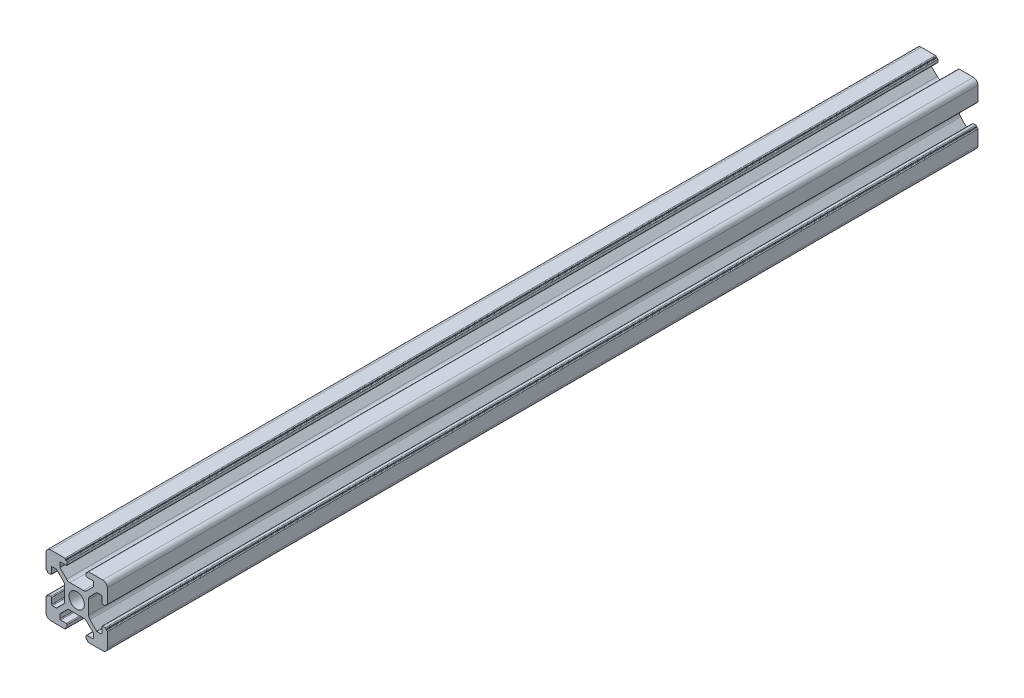
SolidWorks part; units mm, degrees
ref_plane "前视基准面" through (0, 0, 0) normal (0, 0, 1) x (1, 0, 0)
ref_plane "上视基准面" through (0, 0, 0) normal (0, 1, 0) x (1, 0, 0)
ref_plane "右视基准面" through (0, 0, 0) normal (1, 0, 0) x (0, 0, -1)
sketch "草图1" plane through (0, 0, 0) normal (0, 0, 1) x (1, 0, 0)
  line L0 (0, 0) -> (0, 5.5) construction
  line L1 (-8.5023, -10.0023) -> (-3.85, -10.0023)
  line L2 (-10.0023, -8.5023) -> (-10.0023, -3.85)
  line L3 (-8.5023, 10.0023) -> (-3.85, 10.0023)
  line L4 (10.0023, -8.5023) -> (10.0023, -3.85)
  line L5 (-10.0023, -10.0023) -> (10.0023, 10.0023) construction
  line L6 (-10.0023, 10.0023) -> (10.0023, -10.0023) construction
  line L7 (-2.218, -3.9) -> (2.218, -3.9)
  line L8 (-3.9, -2.218) -> (-3.9, 2.218)
  line L9 (-2.218, 3.9) -> (2.218, 3.9)
  line L10 (3.9, -2.218) -> (3.9, 2.218)
  line L11 (-3.9, -3.9) -> (3.9, 3.9) construction
  line L12 (-3.9, 3.9) -> (3.9, -3.9) construction
  line L13 (-5.25, -8.2) -> (-3.35, -8.2)
  line L14 (-8.2, -5.25) -> (-8.2, -3.35)
  line L15 (-5.25, 8.2) -> (-3.35, 8.2)
  line L16 (8.2, -5.25) -> (8.2, -3.35)
  line L17 (-8.2, -8.2) -> (8.2, 8.2) construction
  line L18 (-8.2, 8.2) -> (8.2, -8.2) construction
  line L19 (-7.95, 5.5) -> (-6.6642, 5.5)
  line L20 (0, 0) -> (5.5, 0) construction
  line L23 (-5.5, 7.95) -> (-5.5, 6.6642)
  line L26 (0, 0) -> (-0.5303, 0.5303)
  line L27 (3.2787, 4.3393) -> (5.4268, 6.4874)
  line L28 (0, 0) -> (0.5303, -0.5303)
  line L29 (5.5, 6.6642) -> (5.5, 7.95)
  line L30 (4.3393, 3.2787) -> (6.4874, 5.4268)
  line L31 (6.6642, 5.5) -> (7.95, 5.5)
  line L32 (4.3393, -3.2787) -> (6.4874, -5.4268)
  line L33 (3.2787, -4.3393) -> (5.4268, -6.4874)
  line L34 (-3.2787, -4.3393) -> (-5.4268, -6.4874)
  line L35 (-4.3393, -3.2787) -> (-6.4874, -5.4268)
  line L36 (-4.3393, 3.2787) -> (-6.4874, 5.4268)
  line L37 (-3.2787, 4.3393) -> (-5.4268, 6.4874)
  line L38 (3.1, -8.45) -> (3.1, -9.2523)
  line L39 (8.45, 3.1) -> (9.2523, 3.1)
  line L40 (-5.5, -6.6642) -> (-5.5, -7.95)
  line L41 (-6.6642, -5.5) -> (-7.95, -5.5)
  line L42 (5.5, -6.6642) -> (5.5, -7.95)
  line L43 (6.6642, -5.5) -> (7.95, -5.5)
  line L44 (9.2523, -3.1) -> (8.45, -3.1)
  line L46 (10.0023, 3.85) -> (10.0023, 8.5023)
  line L47 (8.2, 3.35) -> (8.2, 5.25)
  line L48 (-3.1, -9.2523) -> (-3.1, -8.45)
  line L49 (-8.45, -3.1) -> (-9.2523, -3.1)
  line L50 (-9.2523, 3.1) -> (-8.45, 3.1)
  line L51 (-3.1, 8.45) -> (-3.1, 9.2523)
  line L52 (3.1, 9.2523) -> (3.1, 8.45)
  line L53 (3.85, 10.0023) -> (8.5023, 10.0023)
  line L54 (3.35, 8.2) -> (5.25, 8.2)
  line L55 (-10.0023, 3.85) -> (-10.0023, 8.5023)
  line L56 (-8.2, 3.35) -> (-8.2, 5.25)
  line L57 (3.35, -8.2) -> (5.25, -8.2)
  line L58 (3.85, -10.0023) -> (8.5023, -10.0023)
  line L59 (9.7523, -3.6) -> (9.5023, -3.6)
  line L61 (9.7523, 3.6) -> (9.5023, 3.6)
  line L62 (9.5023, -3.6) -> (9.5023, -3.35)
  line L63 (3.6, -9.7523) -> (3.6, -9.5023)
  line L64 (3.35, -9.5023) -> (3.6, -9.5023)
  line L65 (9.5023, 3.35) -> (9.5023, 3.6)
  line L66 (-3.6, -9.5023) -> (-3.35, -9.5023)
  line L67 (-3.6, -9.7523) -> (-3.6, -9.5023)
  line L68 (-9.7523, -3.6) -> (-9.5023, -3.6)
  line L69 (-9.5023, -3.35) -> (-9.5023, -3.6)
  line L70 (-9.5023, 3.6) -> (-9.5023, 3.35)
  line L71 (-9.7523, 3.6) -> (-9.5023, 3.6)
  line L72 (-3.6, 9.7523) -> (-3.6, 9.5023)
  line L73 (-3.35, 9.5023) -> (-3.6, 9.5023)
  line L74 (3.6, 9.5023) -> (3.35, 9.5023)
  line L75 (3.6, 9.7523) -> (3.6, 9.5023)
  circle A0 centre (0, 0) radius 2.5
  arc A1 (10.0023, 8.5023) -> (8.5023, 10.0023) centre (8.5023, 8.5023) ccw
  arc A2 (8.5023, -10.0023) -> (10.0023, -8.5023) centre (8.5023, -8.5023) ccw
  arc A3 (-10.0023, -8.5023) -> (-8.5023, -10.0023) centre (-8.5023, -8.5023) ccw
  arc A4 (-10.0023, 8.5023) -> (-8.5023, 10.0023) centre (-8.5023, 8.5023) cw
  arc A5 (-9.5023, -3.35) -> (-9.2523, -3.1) centre (-9.2523, -3.35) cw
  arc A6 (-9.7523, -3.6) -> (-10.0023, -3.85) centre (-9.7523, -3.85) ccw
  arc A7 (-8.45, -3.1) -> (-8.2, -3.35) centre (-8.45, -3.35) cw
  arc A8 (-7.95, -5.5) -> (-8.2, -5.25) centre (-7.95, -5.25) cw
  arc A9 (-6.4874, -5.4268) -> (-6.6642, -5.5) centre (-6.6642, -5.25) cw
  arc A10 (-5.4268, -6.4874) -> (-5.5, -6.6642) centre (-5.25, -6.6642) ccw
  arc A11 (-5.5, -7.95) -> (-5.25, -8.2) centre (-5.25, -7.95) ccw
  arc A12 (-3.6, -9.7523) -> (-3.85, -10.0023) centre (-3.85, -9.7523) cw
  arc A13 (-3.35, -9.5023) -> (-3.1, -9.2523) centre (-3.35, -9.2523) ccw
  arc A14 (-3.1, -8.45) -> (-3.35, -8.2) centre (-3.35, -8.45) ccw
  arc A15 (3.1, -8.45) -> (3.35, -8.2) centre (3.35, -8.45) cw
  arc A16 (5.5, -7.95) -> (5.25, -8.2) centre (5.25, -7.95) cw
  arc A17 (5.4268, -6.4874) -> (5.5, -6.6642) centre (5.25, -6.6642) cw
  arc A18 (6.4874, -5.4268) -> (6.6642, -5.5) centre (6.6642, -5.25) ccw
  arc A19 (7.95, -5.5) -> (8.2, -5.25) centre (7.95, -5.25) ccw
  arc A20 (8.45, -3.1) -> (8.2, -3.35) centre (8.45, -3.35) ccw
  arc A21 (9.5023, -3.35) -> (9.2523, -3.1) centre (9.2523, -3.35) ccw
  arc A22 (9.7523, -3.6) -> (10.0023, -3.85) centre (9.7523, -3.85) cw
  arc A23 (3.35, -9.5023) -> (3.1, -9.2523) centre (3.35, -9.2523) cw
  arc A24 (3.6, -9.7523) -> (3.85, -10.0023) centre (3.85, -9.7523) ccw
  arc A25 (7.95, 5.5) -> (8.2, 5.25) centre (7.95, 5.25) cw
  arc A26 (8.2, 3.35) -> (8.45, 3.1) centre (8.45, 3.35) ccw
  arc A27 (9.5023, 3.35) -> (9.2523, 3.1) centre (9.2523, 3.35) cw
  arc A28 (9.7523, 3.6) -> (10.0023, 3.85) centre (9.7523, 3.85) ccw
  arc A29 (6.6642, 5.5) -> (6.4874, 5.4268) centre (6.6642, 5.25) ccw
  arc A30 (5.4268, 6.4874) -> (5.5, 6.6642) centre (5.25, 6.6642) ccw
  arc A31 (5.5, 7.95) -> (5.25, 8.2) centre (5.25, 7.95) ccw
  arc A32 (3.1, 8.45) -> (3.35, 8.2) centre (3.35, 8.45) ccw
  arc A33 (3.6, 9.7523) -> (3.85, 10.0023) centre (3.85, 9.7523) cw
  arc A34 (3.35, 9.5023) -> (3.1, 9.2523) centre (3.35, 9.2523) ccw
  arc A35 (-9.7523, 3.6) -> (-10.0023, 3.85) centre (-9.7523, 3.85) cw
  arc A36 (-9.5023, 3.35) -> (-9.2523, 3.1) centre (-9.2523, 3.35) ccw
  arc A37 (-8.45, 3.1) -> (-8.2, 3.35) centre (-8.45, 3.35) ccw
  arc A38 (-8.2, 5.25) -> (-7.95, 5.5) centre (-7.95, 5.25) cw
  arc A39 (-6.4874, 5.4268) -> (-6.6642, 5.5) centre (-6.6642, 5.25) ccw
  arc A40 (-5.4268, 6.4874) -> (-5.5, 6.6642) centre (-5.25, 6.6642) cw
  arc A41 (-5.5, 7.95) -> (-5.25, 8.2) centre (-5.25, 7.95) cw
  arc A42 (-3.1, 8.45) -> (-3.35, 8.2) centre (-3.35, 8.45) cw
  arc A43 (-3.1, 9.2523) -> (-3.35, 9.5023) centre (-3.35, 9.2523) ccw
  arc A44 (-3.6, 9.7523) -> (-3.85, 10.0023) centre (-3.85, 9.7523) ccw
  arc A45 (-4.3393, 3.2787) -> (-3.9, 2.218) centre (-5.4, 2.218) cw
  arc A46 (-3.2787, 4.3393) -> (-2.218, 3.9) centre (-2.218, 5.4) ccw
  arc A47 (3.2787, 4.3393) -> (2.218, 3.9) centre (2.218, 5.4) cw
  arc A48 (4.3393, 3.2787) -> (3.9, 2.218) centre (5.4, 2.218) ccw
  arc A49 (4.3393, -3.2787) -> (3.9, -2.218) centre (5.4, -2.218) cw
  arc A50 (3.2787, -4.3393) -> (2.218, -3.9) centre (2.218, -5.4) ccw
  arc A51 (-4.3393, -3.2787) -> (-3.9, -2.218) centre (-5.4, -2.218) ccw
  arc A52 (-2.218, -3.9) -> (-3.2787, -4.3393) centre (-2.218, -5.4) ccw
  point P0 (0, 0)
  point P7 (10.0023, 0)
  point P62 (0, 0)
  point P76 (0, 0)
  point P92 (-8.2, -5.5)
  point P99 (0, 0)
  point P106 (-5.5, -8.2)
  point P117 (5.5, -8.2)
  point P124 (8.2, -5.5)
  point P137 (8.2, 5.5)
  point P140 (8.2, 3.1)
  point P147 (6.5607, 5.5)
  point P152 (5.5, 8.2)
  point P167 (-8.2, 5.5)
  point P174 (-5.5, 8.2)
  dimension "D1" = 1.5
  dimension "D5" = 0.25
  dimension "D6" = 1.5
  dimension "D2" = 4
  dimension "D3" = 4
  dimension "D4" = 4
extrude "凸台-拉伸1" add sketch "草图1" along normal blind 284 contours A52 L7 A50 L33 A17 L42 A16 L57 A15 L38 A23 L64 L63 A24 L58 A2 L4 A22 L59 L62 A21 L44 A20 L16 A19 L43 A18 L32 A49 L10 A48 L30 A29 L31 A25 L47 A26 L39 A27 L65 L61 A28 L46 A1 L53 A33 L75 L74 A34 L52 A32
ref_plane "Plane1" through (0, 0, 142) normal (0, 0, 1) x (1, 0, 0)
